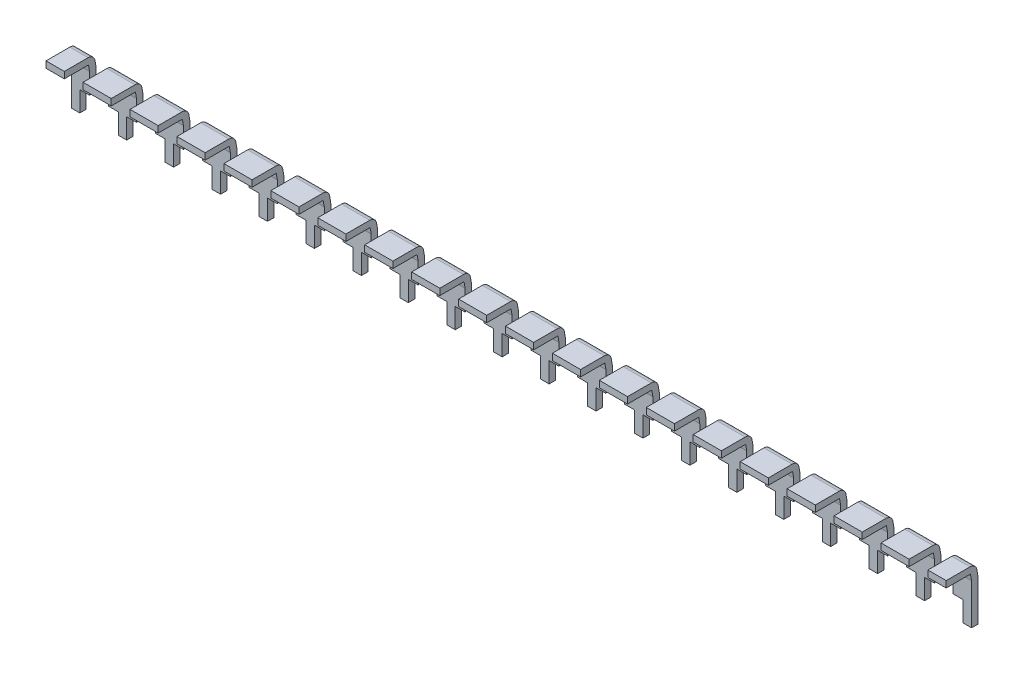
SolidWorks part; units mm, degrees
ref_plane "Front Plane" through (0, 0, 0) normal (0, 0, 1) x (1, 0, 0)
ref_plane "Top Plane" through (0, 0, 0) normal (0, 1, 0) x (1, 0, 0)
ref_plane "Right Plane" through (0, 0, 0) normal (1, 0, 0) x (0, 0, -1)
sketch "Sketch1" plane through (0, 0, 0) normal (0, 0, 1) x (1, 0, 0)
  line L0 (23.368, 0.175) -> (24.892, 0.175) construction
  line L1 (-2.032, 0.175) -> (-0.508, 0.175)
  line L2 (-2.032, 0.175) -> (-2.032, -0.175)
  line L3 (-2.032, -0.175) -> (-0.508, -0.175)
  line L4 (-0.508, 0.175) -> (-0.508, -0.175)
  line L5 (-2.032, 0.175) -> (-0.508, -0.175) construction
  line L6 (-2.032, -0.175) -> (-0.508, 0.175) construction
  line L7 (20.828, 0.175) -> (22.352, 0.175)
  line L8 (20.828, 0.175) -> (20.828, -0.175)
  line L9 (20.828, -0.175) -> (22.352, -0.175)
  line L10 (22.352, 0.175) -> (22.352, -0.175)
  line L11 (20.828, 0.175) -> (22.352, -0.175) construction
  line L12 (20.828, -0.175) -> (22.352, 0.175) construction
  line L13 (23.368, 0.175) -> (23.368, -0.175)
  line L14 (23.368, -0.175) -> (24.892, -0.175) construction
  line L15 (24.892, 0.175) -> (24.892, -0.175) construction
  line L16 (23.368, 0.175) -> (24.892, -0.175) construction
  line L17 (23.368, -0.175) -> (24.892, 0.175) construction
  line L18 (-24.892, 0.175) -> (-23.368, 0.175) construction
  line L19 (-24.892, 0.175) -> (-24.892, -0.175) construction
  line L20 (-24.892, -0.175) -> (-23.368, -0.175) construction
  line L21 (-23.368, 0.175) -> (-23.368, -0.175)
  line L22 (-24.892, 0.175) -> (-23.368, -0.175) construction
  line L23 (-24.892, -0.175) -> (-23.368, 0.175) construction
  line L24 (-24.3586, 0.175) -> (-24.3586, -0.175)
  line L25 (24.3586, 0.175) -> (24.3586, -0.175)
  line L26 (24.3586, 0.175) -> (23.368, 0.175)
  line L27 (24.3586, -0.175) -> (23.368, -0.175)
  line L28 (-23.368, 0.175) -> (-24.3586, 0.175)
  line L29 (-23.368, -0.175) -> (-24.3586, -0.175)
  line L30 (0.508, 0.175) -> (2.032, 0.175)
  line L31 (0.508, 0.175) -> (0.508, -0.175)
  line L32 (0.508, -0.175) -> (2.032, -0.175)
  line L33 (2.032, 0.175) -> (2.032, -0.175)
  line L34 (0.508, 0.175) -> (2.032, -0.175) construction
  line L35 (0.508, -0.175) -> (2.032, 0.175) construction
  line L36 (3.048, 0.175) -> (4.572, 0.175)
  line L37 (3.048, 0.175) -> (3.048, -0.175)
  line L38 (3.048, -0.175) -> (4.572, -0.175)
  line L39 (4.572, 0.175) -> (4.572, -0.175)
  line L40 (3.048, 0.175) -> (4.572, -0.175) construction
  line L41 (3.048, -0.175) -> (4.572, 0.175) construction
  line L42 (5.588, 0.175) -> (7.112, 0.175)
  line L43 (5.588, 0.175) -> (5.588, -0.175)
  line L44 (5.588, -0.175) -> (7.112, -0.175)
  line L45 (7.112, 0.175) -> (7.112, -0.175)
  line L46 (5.588, 0.175) -> (7.112, -0.175) construction
  line L47 (5.588, -0.175) -> (7.112, 0.175) construction
  line L48 (8.128, 0.175) -> (9.652, 0.175)
  line L49 (8.128, 0.175) -> (8.128, -0.175)
  line L50 (8.128, -0.175) -> (9.652, -0.175)
  line L51 (9.652, 0.175) -> (9.652, -0.175)
  line L52 (8.128, 0.175) -> (9.652, -0.175) construction
  line L53 (8.128, -0.175) -> (9.652, 0.175) construction
  line L54 (10.668, 0.175) -> (12.192, 0.175)
  line L55 (10.668, 0.175) -> (10.668, -0.175)
  line L56 (10.668, -0.175) -> (12.192, -0.175)
  line L57 (12.192, 0.175) -> (12.192, -0.175)
  line L58 (10.668, 0.175) -> (12.192, -0.175) construction
  line L59 (10.668, -0.175) -> (12.192, 0.175) construction
  line L60 (13.208, 0.175) -> (14.732, 0.175)
  line L61 (13.208, 0.175) -> (13.208, -0.175)
  line L62 (13.208, -0.175) -> (14.732, -0.175)
  line L63 (14.732, 0.175) -> (14.732, -0.175)
  line L64 (13.208, 0.175) -> (14.732, -0.175) construction
  line L65 (13.208, -0.175) -> (14.732, 0.175) construction
  line L66 (15.748, 0.175) -> (17.272, 0.175)
  line L67 (15.748, 0.175) -> (15.748, -0.175)
  line L68 (15.748, -0.175) -> (17.272, -0.175)
  line L69 (17.272, 0.175) -> (17.272, -0.175)
  line L70 (15.748, 0.175) -> (17.272, -0.175) construction
  line L71 (15.748, -0.175) -> (17.272, 0.175) construction
  line L72 (18.288, 0.175) -> (19.812, 0.175)
  line L73 (18.288, 0.175) -> (18.288, -0.175)
  line L74 (18.288, -0.175) -> (19.812, -0.175)
  line L75 (19.812, 0.175) -> (19.812, -0.175)
  line L76 (18.288, 0.175) -> (19.812, -0.175) construction
  line L77 (18.288, -0.175) -> (19.812, 0.175) construction
  line L78 (-4.572, 0.175) -> (-3.048, 0.175)
  line L79 (-4.572, 0.175) -> (-4.572, -0.175)
  line L80 (-4.572, -0.175) -> (-3.048, -0.175)
  line L81 (-3.048, 0.175) -> (-3.048, -0.175)
  line L82 (-4.572, 0.175) -> (-3.048, -0.175) construction
  line L83 (-4.572, -0.175) -> (-3.048, 0.175) construction
  line L84 (-7.112, 0.175) -> (-5.588, 0.175)
  line L85 (-7.112, 0.175) -> (-7.112, -0.175)
  line L86 (-7.112, -0.175) -> (-5.588, -0.175)
  line L87 (-5.588, 0.175) -> (-5.588, -0.175)
  line L88 (-7.112, 0.175) -> (-5.588, -0.175) construction
  line L89 (-7.112, -0.175) -> (-5.588, 0.175) construction
  line L90 (-9.652, 0.175) -> (-8.128, 0.175)
  line L91 (-9.652, 0.175) -> (-9.652, -0.175)
  line L92 (-9.652, -0.175) -> (-8.128, -0.175)
  line L93 (-8.128, 0.175) -> (-8.128, -0.175)
  line L94 (-9.652, 0.175) -> (-8.128, -0.175) construction
  line L95 (-9.652, -0.175) -> (-8.128, 0.175) construction
  line L96 (-12.192, 0.175) -> (-10.668, 0.175)
  line L97 (-12.192, 0.175) -> (-12.192, -0.175)
  line L98 (-12.192, -0.175) -> (-10.668, -0.175)
  line L99 (-10.668, 0.175) -> (-10.668, -0.175)
  line L100 (-12.192, 0.175) -> (-10.668, -0.175) construction
  line L101 (-12.192, -0.175) -> (-10.668, 0.175) construction
  line L102 (-14.732, 0.175) -> (-13.208, 0.175)
  line L103 (-14.732, 0.175) -> (-14.732, -0.175)
  line L104 (-14.732, -0.175) -> (-13.208, -0.175)
  line L105 (-13.208, 0.175) -> (-13.208, -0.175)
  line L106 (-14.732, 0.175) -> (-13.208, -0.175) construction
  line L107 (-14.732, -0.175) -> (-13.208, 0.175) construction
  line L108 (-17.272, 0.175) -> (-15.748, 0.175)
  line L109 (-17.272, 0.175) -> (-17.272, -0.175)
  line L110 (-17.272, -0.175) -> (-15.748, -0.175)
  line L111 (-15.748, 0.175) -> (-15.748, -0.175)
  line L112 (-17.272, 0.175) -> (-15.748, -0.175) construction
  line L113 (-17.272, -0.175) -> (-15.748, 0.175) construction
  line L114 (-19.812, 0.175) -> (-18.288, 0.175)
  line L115 (-19.812, 0.175) -> (-19.812, -0.175)
  line L116 (-19.812, -0.175) -> (-18.288, -0.175)
  line L117 (-18.288, 0.175) -> (-18.288, -0.175)
  line L118 (-19.812, 0.175) -> (-18.288, -0.175) construction
  line L119 (-19.812, -0.175) -> (-18.288, 0.175) construction
  line L120 (-22.352, 0.175) -> (-20.828, 0.175)
  line L121 (-22.352, 0.175) -> (-22.352, -0.175)
  line L122 (-22.352, -0.175) -> (-20.828, -0.175)
  line L123 (-20.828, 0.175) -> (-20.828, -0.175)
  line L124 (-22.352, 0.175) -> (-20.828, -0.175) construction
  line L125 (-22.352, -0.175) -> (-20.828, 0.175) construction
  point P0 (-1.27, 0)
  point P5 (21.59, 0)
  point P12 (24.13, 0)
  point P17 (-24.13, 0)
  point P26 (-3.81, 0)
  point P27 (1.27, 0)
  point P32 (3.81, 0)
  point P37 (6.35, 0)
  point P42 (8.89, 0)
  point P47 (11.43, 0)
  point P52 (13.97, 0)
  point P57 (16.51, 0)
  point P62 (19.05, 0)
  point P71 (-6.35, 0)
  point P76 (-8.89, 0)
  point P81 (-11.43, 0)
  point P86 (-13.97, 0)
  point P91 (-16.51, 0)
  point P96 (-19.05, 0)
  point P101 (-21.59, 0)
  dimension "D1" = 1.524
  dimension "D2" = 22.86
  dimension "D3" = 1.524
  dimension "D4" = 1.27
  dimension "D5" = 0.35
  dimension "D6" = 0.5334
  dimension "D7" = 0.5334
  dimension "D8" = 22.86
  dimension "D9" = 2.54
  dimension "D10" = 2.54
  dimension "D11" = 2.54
sketch "Sketch2" plane through (0, 0, 0) normal (1, 0, 0) x (0, 0, -1)
  line L0 (0, 0) -> (1.289, 0)
  line L1 (1.545, -0.5175) -> (1.545, -2.725)
  line L2 (1.542, -0.4828) -> (1.486, -0.1653)
  arc A0 (1.289, 0) -> (1.486, -0.1653) centre (1.289, -0.2) cw
  arc A1 (1.542, -0.4828) -> (1.545, -0.5175) centre (1.345, -0.5175) cw
  point P10 (1.545, -0.5)
  dimension "D5" = 0.2
  dimension "D6" = 0.2
  dimension "D1" = 1.545
  dimension "D2" = 10
  dimension "D3" = 2.225
  dimension "D4" = 0.5
sweep "Sweep11" add profiles "Sketch1" path "Sketch2"
sketch "Sketch10" plane through (0, 0.2795, -1.5852) normal (0, 0.1736, -0.9848) x (-1, 0, 0)
  line L1 (-23.9014, -1.8432) -> (-23.368, -1.8432)
  line L2 (-23.9014, -1.8432) -> (-23.9014, -2.9823)
  line L3 (-23.9014, -2.9823) -> (-23.368, -2.9823)
  line L4 (-23.368, -1.8432) -> (-23.368, -2.9823)
  line L5 (-23.9014, -1.8432) -> (-23.368, -2.9823) construction
  line L6 (-23.9014, -2.9823) -> (-23.368, -1.8432) construction
  line L8 (-22.352, -1.8432) -> (-21.8186, -1.8432)
  line L9 (-22.352, -1.8432) -> (-22.352, -2.9823)
  line L10 (-22.352, -2.9823) -> (-21.8186, -2.9823)
  line L11 (-20.828, -1.8432) -> (-20.828, -2.9823)
  line L12 (-22.352, -1.8432) -> (-20.828, -2.9823) construction
  line L13 (-22.352, -2.9823) -> (-20.828, -1.8432) construction
  line L14 (-19.812, -1.8432) -> (-19.2786, -1.8432)
  line L15 (-19.812, -1.8432) -> (-19.812, -2.9823)
  line L16 (-19.812, -2.9823) -> (-19.2786, -2.9823)
  line L17 (-18.288, -1.8432) -> (-18.288, -2.9823)
  line L18 (-19.2786, -1.8432) -> (-19.2786, -2.9823)
  line L19 (-18.8214, -1.8432) -> (-18.8214, -2.9823)
  line L20 (23.9014, -1.8432) -> (23.368, -1.8432)
  line L21 (23.9014, -1.8432) -> (23.9014, -2.9823)
  line L22 (23.9014, -2.9823) -> (23.368, -2.9823)
  line L23 (23.368, -1.8432) -> (23.368, -2.9823)
  line L24 (23.9014, -1.8432) -> (23.368, -2.9823) construction
  line L25 (23.9014, -2.9823) -> (23.368, -1.8432) construction
  line L28 (-22.352, -0.8083) -> (-22.352, -2.9823) construction
  line L32 (-21.8186, -1.8432) -> (-21.8186, -2.9823)
  line L33 (-21.3614, -1.8432) -> (-21.3614, -2.9823)
  line L34 (-18.8214, -1.8432) -> (-18.288, -1.8432)
  line L35 (-18.8214, -2.9823) -> (-18.288, -2.9823)
  line L36 (-21.3614, -1.8432) -> (-20.828, -1.8432)
  line L37 (-21.3614, -2.9823) -> (-20.828, -2.9823)
  line L38 (-19.812, -1.8432) -> (-18.288, -2.9823) construction
  line L39 (-19.812, -2.9823) -> (-18.288, -1.8432) construction
  line L41 (-23.368, -0.8083) -> (-23.368, -2.9823) construction
  line L42 (23.368, -0.8083) -> (23.368, -2.9823) construction
  line L43 (23.368, -2.9823) -> (24.3586, -2.9823) construction
  line L44 (-24.3586, -2.9823) -> (-23.368, -2.9823) construction
  line L45 (-17.272, -1.8432) -> (-16.7386, -1.8432)
  line L46 (-17.272, -1.8432) -> (-17.272, -2.9823)
  line L47 (-17.272, -2.9823) -> (-16.7386, -2.9823)
  line L48 (-15.748, -1.8432) -> (-15.748, -2.9823)
  line L49 (-16.7386, -1.8432) -> (-16.7386, -2.9823)
  line L50 (-16.2814, -1.8432) -> (-16.2814, -2.9823)
  line L51 (-16.2814, -1.8432) -> (-15.748, -1.8432)
  line L52 (-16.2814, -2.9823) -> (-15.748, -2.9823)
  line L53 (-17.272, -1.8432) -> (-15.748, -2.9823) construction
  line L54 (-17.272, -2.9823) -> (-15.748, -1.8432) construction
  line L55 (-14.732, -1.8432) -> (-14.1986, -1.8432)
  line L56 (-14.732, -1.8432) -> (-14.732, -2.9823)
  line L57 (-14.732, -2.9823) -> (-14.1986, -2.9823)
  line L58 (-13.208, -1.8432) -> (-13.208, -2.9823)
  line L59 (-14.1986, -1.8432) -> (-14.1986, -2.9823)
  line L60 (-13.7414, -1.8432) -> (-13.7414, -2.9823)
  line L61 (-13.7414, -1.8432) -> (-13.208, -1.8432)
  line L62 (-13.7414, -2.9823) -> (-13.208, -2.9823)
  line L63 (-14.732, -1.8432) -> (-13.208, -2.9823) construction
  line L64 (-14.732, -2.9823) -> (-13.208, -1.8432) construction
  line L65 (-12.192, -1.8432) -> (-11.6586, -1.8432)
  line L66 (-12.192, -1.8432) -> (-12.192, -2.9823)
  line L67 (-12.192, -2.9823) -> (-11.6586, -2.9823)
  line L68 (-10.668, -1.8432) -> (-10.668, -2.9823)
  line L69 (-11.6586, -1.8432) -> (-11.6586, -2.9823)
  line L70 (-11.2014, -1.8432) -> (-11.2014, -2.9823)
  line L71 (-11.2014, -1.8432) -> (-10.668, -1.8432)
  line L72 (-11.2014, -2.9823) -> (-10.668, -2.9823)
  line L73 (-12.192, -1.8432) -> (-10.668, -2.9823) construction
  line L74 (-12.192, -2.9823) -> (-10.668, -1.8432) construction
  line L75 (-9.652, -1.8432) -> (-9.1186, -1.8432)
  line L76 (-9.652, -1.8432) -> (-9.652, -2.9823)
  line L77 (-9.652, -2.9823) -> (-9.1186, -2.9823)
  line L78 (-8.128, -1.8432) -> (-8.128, -2.9823)
  line L79 (-9.1186, -1.8432) -> (-9.1186, -2.9823)
  line L80 (-8.6614, -1.8432) -> (-8.6614, -2.9823)
  line L81 (-8.6614, -1.8432) -> (-8.128, -1.8432)
  line L82 (-8.6614, -2.9823) -> (-8.128, -2.9823)
  line L83 (-9.652, -1.8432) -> (-8.128, -2.9823) construction
  line L84 (-9.652, -2.9823) -> (-8.128, -1.8432) construction
  line L85 (-7.112, -1.8432) -> (-6.5786, -1.8432)
  line L86 (-7.112, -1.8432) -> (-7.112, -2.9823)
  line L87 (-7.112, -2.9823) -> (-6.5786, -2.9823)
  line L88 (-5.588, -1.8432) -> (-5.588, -2.9823)
  line L89 (-6.5786, -1.8432) -> (-6.5786, -2.9823)
  line L90 (-6.1214, -1.8432) -> (-6.1214, -2.9823)
  line L91 (-6.1214, -1.8432) -> (-5.588, -1.8432)
  line L92 (-6.1214, -2.9823) -> (-5.588, -2.9823)
  line L93 (-7.112, -1.8432) -> (-5.588, -2.9823) construction
  line L94 (-7.112, -2.9823) -> (-5.588, -1.8432) construction
  line L95 (-4.572, -1.8432) -> (-4.0386, -1.8432)
  line L96 (-4.572, -1.8432) -> (-4.572, -2.9823)
  line L97 (-4.572, -2.9823) -> (-4.0386, -2.9823)
  line L98 (-3.048, -1.8432) -> (-3.048, -2.9823)
  line L99 (-4.0386, -1.8432) -> (-4.0386, -2.9823)
  line L100 (-3.5814, -1.8432) -> (-3.5814, -2.9823)
  line L101 (-3.5814, -1.8432) -> (-3.048, -1.8432)
  line L102 (-3.5814, -2.9823) -> (-3.048, -2.9823)
  line L103 (-4.572, -1.8432) -> (-3.048, -2.9823) construction
  line L104 (-4.572, -2.9823) -> (-3.048, -1.8432) construction
  line L105 (-2.032, -1.8432) -> (-1.4986, -1.8432)
  line L106 (-2.032, -1.8432) -> (-2.032, -2.9823)
  line L107 (-2.032, -2.9823) -> (-1.4986, -2.9823)
  line L108 (-0.508, -1.8432) -> (-0.508, -2.9823)
  line L109 (-1.4986, -1.8432) -> (-1.4986, -2.9823)
  line L110 (-1.0414, -1.8432) -> (-1.0414, -2.9823)
  line L111 (-1.0414, -1.8432) -> (-0.508, -1.8432)
  line L112 (-1.0414, -2.9823) -> (-0.508, -2.9823)
  line L113 (-2.032, -1.8432) -> (-0.508, -2.9823) construction
  line L114 (-2.032, -2.9823) -> (-0.508, -1.8432) construction
  line L115 (0.508, -1.8432) -> (1.0414, -1.8432)
  line L116 (0.508, -1.8432) -> (0.508, -2.9823)
  line L117 (0.508, -2.9823) -> (1.0414, -2.9823)
  line L118 (2.032, -1.8432) -> (2.032, -2.9823)
  line L119 (1.0414, -1.8432) -> (1.0414, -2.9823)
  line L120 (1.4986, -1.8432) -> (1.4986, -2.9823)
  line L121 (1.4986, -1.8432) -> (2.032, -1.8432)
  line L122 (1.4986, -2.9823) -> (2.032, -2.9823)
  line L123 (0.508, -1.8432) -> (2.032, -2.9823) construction
  line L124 (0.508, -2.9823) -> (2.032, -1.8432) construction
  line L125 (3.048, -1.8432) -> (3.5814, -1.8432)
  line L126 (3.048, -1.8432) -> (3.048, -2.9823)
  line L127 (3.048, -2.9823) -> (3.5814, -2.9823)
  line L128 (4.572, -1.8432) -> (4.572, -2.9823)
  line L129 (3.5814, -1.8432) -> (3.5814, -2.9823)
  line L130 (4.0386, -1.8432) -> (4.0386, -2.9823)
  line L131 (4.0386, -1.8432) -> (4.572, -1.8432)
  line L132 (4.0386, -2.9823) -> (4.572, -2.9823)
  line L133 (3.048, -1.8432) -> (4.572, -2.9823) construction
  line L134 (3.048, -2.9823) -> (4.572, -1.8432) construction
  line L135 (5.588, -1.8432) -> (6.1214, -1.8432)
  line L136 (5.588, -1.8432) -> (5.588, -2.9823)
  line L137 (5.588, -2.9823) -> (6.1214, -2.9823)
  line L138 (7.112, -1.8432) -> (7.112, -2.9823)
  line L139 (6.1214, -1.8432) -> (6.1214, -2.9823)
  line L140 (6.5786, -1.8432) -> (6.5786, -2.9823)
  line L141 (6.5786, -1.8432) -> (7.112, -1.8432)
  line L142 (6.5786, -2.9823) -> (7.112, -2.9823)
  line L143 (5.588, -1.8432) -> (7.112, -2.9823) construction
  line L144 (5.588, -2.9823) -> (7.112, -1.8432) construction
  line L145 (8.128, -1.8432) -> (8.6614, -1.8432)
  line L146 (8.128, -1.8432) -> (8.128, -2.9823)
  line L147 (8.128, -2.9823) -> (8.6614, -2.9823)
  line L148 (9.652, -1.8432) -> (9.652, -2.9823)
  line L149 (8.6614, -1.8432) -> (8.6614, -2.9823)
  line L150 (9.1186, -1.8432) -> (9.1186, -2.9823)
  line L151 (9.1186, -1.8432) -> (9.652, -1.8432)
  line L152 (9.1186, -2.9823) -> (9.652, -2.9823)
  line L153 (8.128, -1.8432) -> (9.652, -2.9823) construction
  line L154 (8.128, -2.9823) -> (9.652, -1.8432) construction
  line L155 (10.668, -1.8432) -> (11.2014, -1.8432)
  line L156 (10.668, -1.8432) -> (10.668, -2.9823)
  line L157 (10.668, -2.9823) -> (11.2014, -2.9823)
  line L158 (12.192, -1.8432) -> (12.192, -2.9823)
  line L159 (11.2014, -1.8432) -> (11.2014, -2.9823)
  line L160 (11.6586, -1.8432) -> (11.6586, -2.9823)
  line L161 (11.6586, -1.8432) -> (12.192, -1.8432)
  line L162 (11.6586, -2.9823) -> (12.192, -2.9823)
  line L163 (10.668, -1.8432) -> (12.192, -2.9823) construction
  line L164 (10.668, -2.9823) -> (12.192, -1.8432) construction
  line L165 (13.208, -1.8432) -> (13.7414, -1.8432)
  line L166 (13.208, -1.8432) -> (13.208, -2.9823)
  line L167 (13.208, -2.9823) -> (13.7414, -2.9823)
  line L168 (14.732, -1.8432) -> (14.732, -2.9823)
  line L169 (13.7414, -1.8432) -> (13.7414, -2.9823)
  line L170 (14.1986, -1.8432) -> (14.1986, -2.9823)
  line L171 (14.1986, -1.8432) -> (14.732, -1.8432)
  line L172 (14.1986, -2.9823) -> (14.732, -2.9823)
  line L173 (13.208, -1.8432) -> (14.732, -2.9823) construction
  line L174 (13.208, -2.9823) -> (14.732, -1.8432) construction
  line L175 (15.748, -1.8432) -> (16.2814, -1.8432)
  line L176 (15.748, -1.8432) -> (15.748, -2.9823)
  line L177 (15.748, -2.9823) -> (16.2814, -2.9823)
  line L178 (17.272, -1.8432) -> (17.272, -2.9823)
  line L179 (16.2814, -1.8432) -> (16.2814, -2.9823)
  line L180 (16.7386, -1.8432) -> (16.7386, -2.9823)
  line L181 (16.7386, -1.8432) -> (17.272, -1.8432)
  line L182 (16.7386, -2.9823) -> (17.272, -2.9823)
  line L183 (15.748, -1.8432) -> (17.272, -2.9823) construction
  line L184 (15.748, -2.9823) -> (17.272, -1.8432) construction
  line L185 (18.288, -1.8432) -> (18.8214, -1.8432)
  line L186 (18.288, -1.8432) -> (18.288, -2.9823)
  line L187 (18.288, -2.9823) -> (18.8214, -2.9823)
  line L188 (19.812, -1.8432) -> (19.812, -2.9823)
  line L189 (18.8214, -1.8432) -> (18.8214, -2.9823)
  line L190 (19.2786, -1.8432) -> (19.2786, -2.9823)
  line L191 (19.2786, -1.8432) -> (19.812, -1.8432)
  line L192 (19.2786, -2.9823) -> (19.812, -2.9823)
  line L193 (18.288, -1.8432) -> (19.812, -2.9823) construction
  line L194 (18.288, -2.9823) -> (19.812, -1.8432) construction
  line L195 (20.828, -1.8432) -> (21.3614, -1.8432)
  line L196 (20.828, -1.8432) -> (20.828, -2.9823)
  line L197 (20.828, -2.9823) -> (21.3614, -2.9823)
  line L198 (22.352, -1.8432) -> (22.352, -2.9823)
  line L199 (21.3614, -1.8432) -> (21.3614, -2.9823)
  line L200 (21.8186, -1.8432) -> (21.8186, -2.9823)
  line L201 (21.8186, -1.8432) -> (22.352, -1.8432)
  line L202 (21.8186, -2.9823) -> (22.352, -2.9823)
  line L203 (20.828, -1.8432) -> (22.352, -2.9823) construction
  line L204 (20.828, -2.9823) -> (22.352, -1.8432) construction
  line L205 (-24.3586, -0.7432) -> (-23.368, -0.7432) construction
  point P0 (-23.6347, -2.4127)
  point P6 (-21.59, -2.4127)
  point P16 (-19.05, -2.4127)
  point P21 (23.6347, -2.4127)
  point P44 (-16.51, -2.4127)
  point P55 (-13.97, -2.4127)
  point P64 (-11.43, -2.4127)
  point P73 (-8.89, -2.4127)
  point P82 (-6.35, -2.4127)
  point P91 (-3.81, -2.4127)
  point P100 (-1.27, -2.4127)
  point P109 (1.27, -2.4127)
  point P118 (3.81, -2.4127)
  point P127 (6.35, -2.4127)
  point P136 (8.89, -2.4127)
  point P145 (11.43, -2.4127)
  point P154 (13.97, -2.4127)
  point P163 (16.51, -2.4127)
  point P172 (19.05, -2.4127)
  point P181 (21.59, -2.4127)
  dimension "D1" = 0.5334
  dimension "D2" = 0.5334
  dimension "D3" = 0.4572
  dimension "D4" = 2.54
  dimension "D5" = 1.1
  dimension "D6" = 0.2286
extrude "Extrude1" cut sketch "Sketch10" against normal through all
